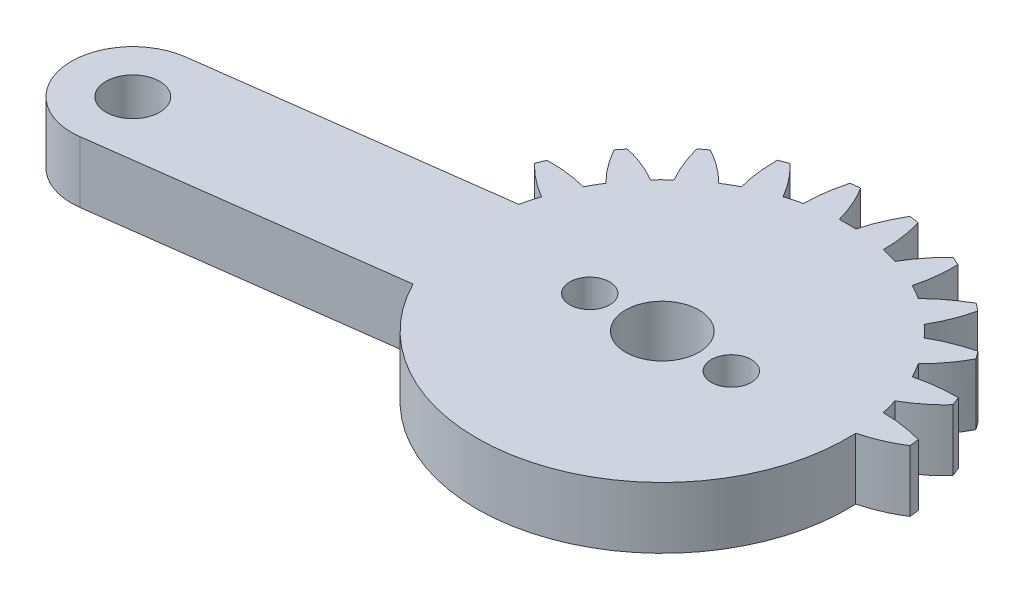
SolidWorks part; units mm, degrees
ref_plane "Alzado" through (0, 0, 0) normal (0, 0, 1) x (1, 0, 0)
ref_plane "Planta" through (0, 0, 0) normal (0, 1, 0) x (1, 0, 0)
ref_plane "Vista lateral" through (0, 0, 0) normal (1, 0, 0) x (0, 0, -1)
sketch "Croquis1" plane through (0, 0, 0) normal (0, 1, 0) x (1, 0, 0)
  line L3 (-10.7781, -5.4652) -> (-29.957, -7.9998)
  line L5 (-31.0067, -0.057) -> (-11.8278, 2.4777)
  circle A0 centre (0, 0) radius 2.3915
  circle A1 centre (4.5, 0) radius 1.3
  circle A2 centre (-4.494, -0.2323) radius 1.3
  arc A3 (-10.7781, -5.4652) -> (-11.8278, 2.4777) centre (0, 0) ccw
  arc A4 (-31.0067, -0.057) -> (-29.957, -7.9998) centre (-30.4818, -4.0284) ccw
  circle A5 centre (-30.4818, -4.0284) radius 1.75
  point P8 (-10.0697, 2.71)
  point P9 (-9.02, -5.2329)
  dimension "D1" = 24.169
  dimension "D2" = 4.783
  dimension "D3" = 2.6
  dimension "D4" = 2.6
  dimension "D13" = 3.5
  dimension "D5" = 4.5
  dimension "D6" = 4.5
  dimension "D8" = 4.526
  dimension "D9" = 10.428
  dimension "D11" = 10.428
extrude "Saliente-Extruir1" add sketch "Croquis1" along normal blind 4
sketch "Croquis2" plane through (0, 0, 0) normal (0, 1, 0) x (1, 0, 0)
  line L0 (-13.3959, 5.8764) -> (-13.6445, 5.304)
  line L1 (-11.8278, 2.4777) -> (-31.0067, -0.057) construction
  arc A0 (-10.7781, -5.4652) -> (-11.8278, 2.4777) centre (0, 0) ccw construction
  spline S0 degree 2 poles (-11.5196, 3.6517) (-12.5723, 4.2394) (-13.6445, 5.304) knots 0 0 0 0.551059 0.551059 0.551059
  spline S1 degree 2 poles (-10.7241, 5.5703) (-12.0679, 5.9342) (-13.3959, 5.8764) knots 0 0 0 0.450011 0.450011 0.450011
  spline S2 degree 2 poles (-11.5196, 3.6517) (-11.2023, 4.6497) (-10.7241, 5.5703) knots 0 0 0 0.773723 0.773723 0.773723
  point P0 (-11.8278, 2.4777)
  point P1 (-11.5196, 3.6517)
  point P3 (-10.7241, 5.5703)
  dimension "D4" = 2.7
  dimension "D5" = 2.7
  dimension "D1" = 1.174
  dimension "D2" = 2.077
  dimension "D3" = 0.624
  dimension "D6" = 3.04
extrude "Saliente-Extruir2" add sketch "Croquis2" along normal blind 4
pattern_circular "MatrizC1" count 2 every 15 of "Saliente-Extruir2"
pattern_circular "MatrizC2" count 2 every 15 of "MatrizC1"
pattern_circular "MatrizC3" count 2 every 15 of "MatrizC2"
pattern_circular "MatrizC4" count 2 every 15 of "MatrizC3"
pattern_circular "MatrizC5" count 2 every 15 of "MatrizC4"
pattern_circular "MatrizC6" count 2 every 15 of "MatrizC5"
pattern_circular "MatrizC7" count 2 every 15 of "MatrizC6"
pattern_circular "MatrizC8" count 2 every 15 of "MatrizC7"
pattern_circular "MatrizC9" count 2 every 15 of "MatrizC8"
pattern_circular "MatrizC10" count 2 every 15 of "MatrizC9"
sketch "Croquis3" plane through (0, 4, 0) normal (0, 1, 0) x (1, 0, 0)
  point P1 (12.0725, 0.538)
